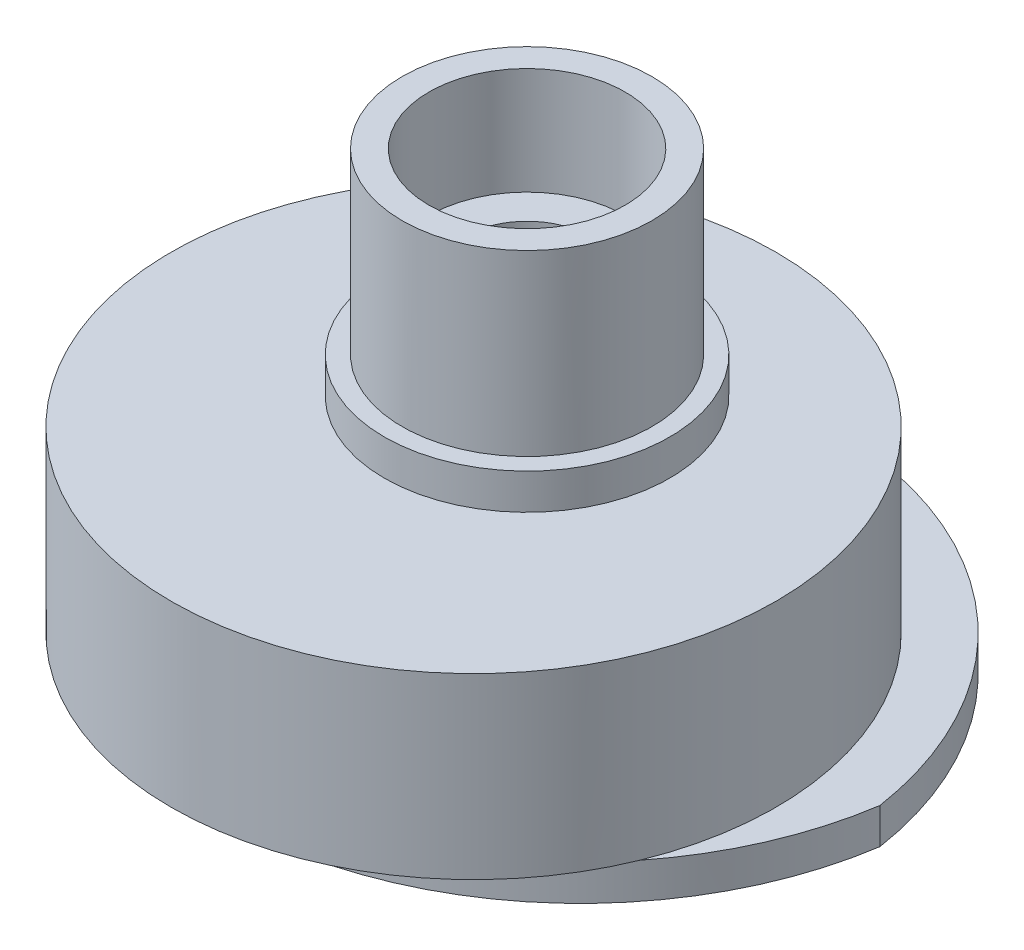
SolidWorks part; units mm, degrees
ref_plane "Front Plane" through (0, 0, 0) normal (0, 0, 1) x (1, 0, 0)
ref_plane "Top Plane" through (0, 0, 0) normal (0, 1, 0) x (1, 0, 0)
ref_plane "Right Plane" through (0, 0, 0) normal (1, 0, 0) x (0, 0, -1)
sketch "Sketch1" plane through (0, 0, 0) normal (0, 1, 0) x (1, 0, 0)
  circle A0 centre (0, 0) radius 3.5
  circle A1 centre (0, 0) radius 2.75
  dimension "D1" = 7
  dimension "D2" = 5.5
extrude "Boss-Extrude1" add sketch "Sketch1" along normal blind 3
sketch "Sketch2" plane through (0, 0, 0) normal (0, -1, 0) x (-1, 0, 0)
  circle A0 centre (0, 0) radius 3.5 construction
  circle A1 centre (0, 0) radius 3.5
  circle A2 centre (0, 0) radius 1.75
  dimension "D1" = 3.5
extrude "Boss-Extrude2" add sketch "Sketch2" along normal blind 2
sketch "Sketch3" plane through (0, -2, 0) normal (0, -1, 0) x (-1, 0, 0)
  circle A0 centre (0, 0) radius 1.75 construction
  circle A1 centre (0, 0) radius 1.75
  circle A2 centre (0, 0) radius 4
  dimension "D1" = 8
extrude "Boss-Extrude3" add sketch "Sketch3" along normal blind 1
sketch "Sketch4" plane through (0, -3, 0) normal (0, -1, 0) x (-1, 0, 0)
  circle A0 centre (0, -1.5) radius 8.475
  circle A1 centre (0, 0) radius 1.75 construction
  circle A2 centre (0, 0) radius 1.75
  dimension "D2" = 16.95
  dimension "D1" = 1.5
extrude "Boss-Extrude4" add sketch "Sketch4" along normal blind 5
sketch "Sketch5" plane through (0, -8, 0) normal (0, -1, 0) x (-1, 0, 0)
  arc A2 (-9.8869, 0) -> (9.8869, 0) centre (0, 1.5) ccw
  arc A3 (9.8869, 0) -> (-9.8869, 0) centre (0, -1.5) ccw
  circle A4 centre (0, 0) radius 1.75 construction
  circle A5 centre (0, 0) radius 1.75
  dimension "D1" = 1.5
  dimension "D2" = 20
  dimension "D3" = 20
extrude "Boss-Extrude5" add sketch "Sketch5" along normal blind 1
sketch "Sketch6" plane through (0, -9, 0) normal (0, -1, 0) x (-1, 0, 0)
  line L1 (4.65, 3.15) -> (-4.65, 3.15)
  line L2 (4.65, 3.15) -> (4.65, -3.15)
  line L3 (4.65, -3.15) -> (-4.65, -3.15)
  line L4 (-4.65, 3.15) -> (-4.65, -3.15)
  line L5 (4.65, 3.15) -> (-4.65, -3.15) construction
  line L6 (4.65, -3.15) -> (-4.65, 3.15) construction
  point P0 (0, 0)
  dimension "D1" = 9.3
  dimension "D2" = 6.3
extrude "Cut-Extrude1" cut sketch "Sketch6" against normal blind 5
